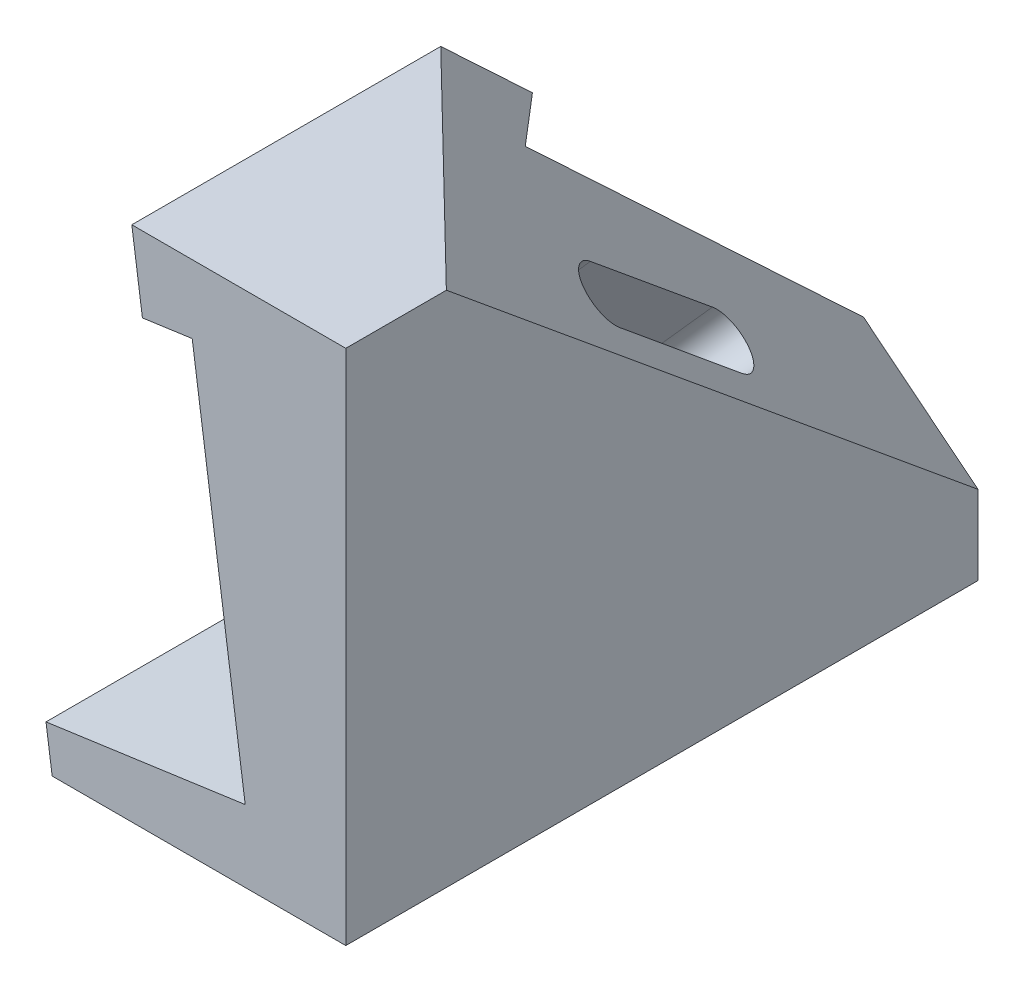
SolidWorks part; units mm, degrees
material "6061 Alloy"
ref_plane "Front Plane" through (0, 0, 0) normal (0, 0, 1) x (1, 0, 0)
ref_plane "Top Plane" through (0, 0, 0) normal (0, 1, 0) x (1, 0, 0)
ref_plane "Right Plane" through (0, 0, 0) normal (1, 0, 0) x (0, 0, -1)
sketch "Sketch2" plane through (0, 0, 0) normal (0, 0, 1) x (1, 0, 0)
  line L0 (21.7383, 28.0735) -> (21.7383, -43.9265)
  line L1 (21.7383, -43.9265) -> (-19.1314, -43.9265)
  line L2 (-19.1314, -43.9265) -> (-19.9892, -37.8233)
  line L3 (0.3622, 18.5577) -> (7.7383, -33.9265)
  line L4 (7.7383, -33.9265) -> (-19.9892, -37.8233)
  line L5 (0.3622, 18.5577) -> (-6.5697, 17.5835)
  line L6 (-6.5697, 17.5835) -> (-8.044, 28.0735)
  line L7 (-8.044, 28.0735) -> (21.7383, 28.0735)
  dimension "D1" = 72
  dimension "D2" = 28
  dimension "D3" = 53
  dimension "D4" = 8
  dimension "D5" = 10
  dimension "D6" = 8
  dimension "D7" = 7
  dimension "D8" = 14
extrude "Boss-Extrude1" add sketch "Sketch2" against normal blind 88 contours L3 L4 L2 L1 L0 L7 L6 L5
sketch "Sketch3" plane through (0, 28.0735, 0) normal (0, 1, 0) x (1, 0, 0)
  line L0 (21.7383, 88) -> (21.7383, 0) construction
  line L1 (-8.044, 88) -> (-8.044, 0) construction
  line L2 (-8.044, 88) -> (21.7383, 88) construction
  point P0 (21.7383, 14)
  point P1 (-8.044, 43)
  dimension "D1" = 14
  dimension "D2" = 45
sketch "Sketch4" plane through (21.7383, 0, 0) normal (1, 0, 0) x (0, 0, -1)
  line L0 (88, 28.0735) -> (88, -43.9265) construction
  line L1 (88, -43.9265) -> (0, -43.9265) construction
  point P0 (88, -32.9265)
  dimension "D1" = 11
ref_plane "Plane1" through (19.7103, 24.5559, -20.242) normal (-0.5265, -0.656, 0.5408) x (-0.8501, 0.4063, -0.3349)
sketch "Sketch5" plane through (19.7103, 24.5559, -20.242) normal (-0.5265, -0.656, 0.5408) x (-0.8501, 0.4063, -0.3349)
  line L1 (78.2934, -61.7835) -> (-42.0209, -61.7835)
  line L2 (78.2934, -61.7835) -> (78.2934, 144.141)
  line L3 (78.2934, 144.141) -> (-42.0209, 144.141)
  line L4 (-42.0209, -61.7835) -> (-42.0209, 144.141)
  line L5 (78.2934, -61.7835) -> (-42.0209, 144.141) construction
  line L6 (78.2934, 144.141) -> (-42.0209, -61.7835) construction
  point P0 (18.1362, 41.1787)
extrude "Cut-Extrude1" cut sketch "Sketch5" against normal blind 88
sketch "Sketch6" plane through (19.7103, 24.5559, -20.242) normal (0.5265, 0.656, -0.5408) x (0.8501, -0.4063, 0.3349)
  line L0 (-1.6145, 26.946) -> (-1.6145, 48.946)
  line L1 (-9.6145, 26.946) -> (-9.6145, 48.946)
  line L2 (2.3855, 88.847) -> (2.3855, -7.054) construction
  arc A0 (-9.6145, 26.946) -> (-1.6145, 26.946) centre (-5.6145, 26.946) ccw
  arc A1 (-1.6145, 48.946) -> (-9.6145, 48.946) centre (-5.6145, 48.946) ccw
  point P1 (-5.6145, 22.946)
  point P3 (-5.6145, 52.946)
  dimension "D1" = 8
  dimension "D2" = 8
  dimension "D3" = 30
  dimension "D4" = 30
  dimension "D5" = 4
extrude "Cut-Extrude2" cut sketch "Sketch6" against normal up to surface (13.238 mm away)
